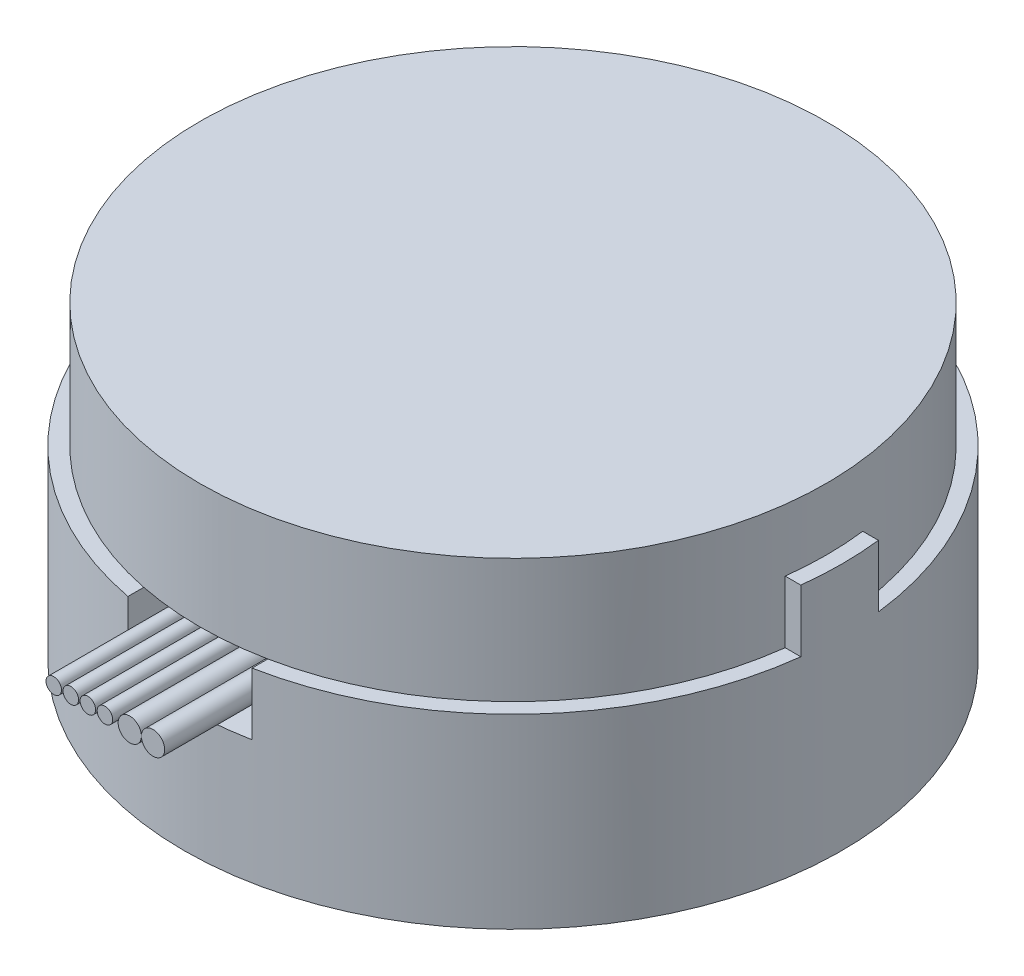
SolidWorks part; units mm, degrees
material "CA"
ref_plane "Front" through (0, 0, 0) normal (0, 0, 1) x (1, 0, 0)
ref_plane "Top" through (0, 0, 0) normal (0, 1, 0) x (1, 0, 0)
ref_plane "Right" through (0, 0, 0) normal (1, 0, 0) x (0, 0, -1)
sketch "Sketch1" plane through (0, 0, 0) normal (0, 1, 0) x (1, 0, 0)
  circle A0 centre (0, 0) radius 21.2
  dimension "D1" = 42.4
extrude "Boss-Extrude1" add sketch "Sketch1" along normal blind 20
sketch "Sketch2" plane through (0, 20, 0) normal (0, 1, 0) x (1, 0, 0)
  circle A0 centre (0, 0) radius 20.2
  dimension "D1" = 40.4
extrude "Cut-Extrude1" cut sketch "Sketch2" against normal offset from surface (4 mm away) 16 flip side to cut contours A0 up to face at (0, 0, 21.2)
sketch "Sketch3" plane through (0, 16, 0) normal (0, 1, 0) x (1, 0, 0)
  line L0 (20.0447, 2.5) -> (23.0373, 2.5)
  line L1 (-23.0373, -2.5) -> (-20.0447, -2.5)
  line L2 (-23.0373, -2.5) -> (-23.0373, 2.5)
  line L3 (-23.0373, 2.5) -> (-20.0447, 2.5)
  line L4 (23.0373, -2.5) -> (23.0373, 2.5)
  line L9 (20.0447, -2.5) -> (23.0373, -2.5)
  arc A0 (20.0447, 2.5) -> (-20.0447, 2.5) centre (0, 0) ccw
  arc A1 (-20.0447, -2.5) -> (20.0447, -2.5) centre (0, 0) ccw
  dimension "D1" = 5
extrude "Cut-Extrude2" cut sketch "Sketch3" against normal blind 4 flip side to cut
ref_plane "Plane1" through (0, 0, 21.2) normal (0, 0, 1) x (1, 0, 0)
sketch "Sketch4" plane through (0, 0, 21.2) normal (0, 0, 1) x (1, 0, 0)
  line L0 (21.0521, 12) -> (-21.0521, 12) construction
  line L1 (-4, 12) -> (4, 12)
  line L2 (-4, 12) -> (-4, 8)
  line L3 (-4, 8) -> (4, 8)
  line L4 (4, 12) -> (4, 8)
  line L5 (-4, 12) -> (4, 8) construction
  line L6 (-4, 8) -> (4, 12) construction
  point P0 (0, 10)
  dimension "D1" = 8
extrude "Cut-Extrude3" cut sketch "Sketch4" against normal blind 5
sketch "Sketch5" plane through (0, 0, 16.2) normal (0, 0, 1) x (1, 0, 0)
  line L1 (4, 12) -> (4, 8) construction
  line L2 (-4, 8) -> (-4, 12) construction
  circle A0 centre (3, 10.0171) radius 0.75
  circle A1 centre (1.5, 10.0171) radius 0.75
  circle A2 centre (-3.4, 10.0171) radius 0.5
  circle A3 centre (-2.3, 10.0171) radius 0.5
  circle A4 centre (-1.2, 10.0171) radius 0.5
  circle A5 centre (-0.1, 10.0171) radius 0.5
  dimension "D2" = 1.5
  dimension "D4" = 1
  dimension "D5" = 0.6
  dimension "D1" = 1
  dimension "D3" = 2
  dimension "D6" = 4
extrude "Boss-Extrude3" add sketch "Sketch5" along normal blind 10 separate body contours A2 | A3 | A4 | A5 | A1 | A0
